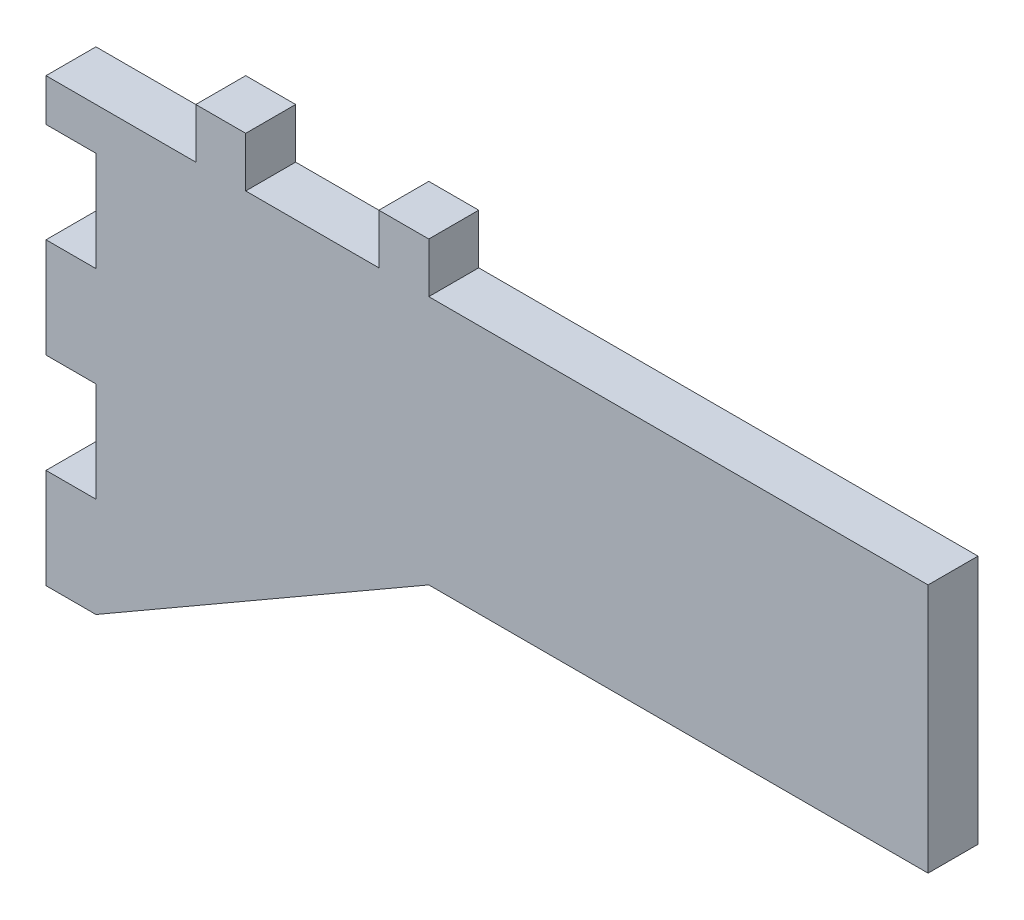
SolidWorks part; units mm, degrees
ref_plane "Front Plane" through (0, 0, 0) normal (0, 0, 1) x (1, 0, 0)
ref_plane "Top Plane" through (0, 0, 0) normal (0, 1, 0) x (1, 0, 0)
ref_plane "Right Plane" through (0, 0, 0) normal (1, 0, 0) x (0, 0, -1)
sketch "Sketch1" plane through (0, 0, 0) normal (0, 0, 1) x (1, 0, 0)
  line L0 (-49.8398, 0) -> (53.8215, 0) construction
  line L1 (0, 44.3135) -> (0, -40.4691) construction
  line L2 (-3, 0) -> (-11, 0)
  line L3 (0, 0) -> (30, 0)
  line L5 (0, -15) -> (30, -15)
  line L6 (30, 0) -> (30, -15)
  line L7 (-20, 0) -> (-20, -26.54)
  line L8 (-20, -26.54) -> (0, -15)
  line L9 (-14, 0) -> (-20, 0)
  line L11 (0, 0) -> (0, 3)
  line L12 (0, 3) -> (-3, 3)
  line L13 (-3, 0) -> (-3, 3)
  line L15 (-11, 0) -> (-11, 3)
  line L16 (-11, 3) -> (-14, 3)
  line L17 (-14, 0) -> (-14, 3)
  point P18 (0, 1.5)
  dimension "D1" = 30
  dimension "D2" = 15
  dimension "D3" = 150.015
  dimension "D4" = 20
  dimension "D5" = 3
  dimension "D6" = 3
  dimension "D7" = 8
  dimension "D8" = 3
  dimension "D9" = 3
extrude "Boss-Extrude1" add sketch "Sketch1" along normal blind 3
sketch "Sketch2" plane through (0, 0, 3) normal (0, 0, 1) x (1, 0, 0)
  line L0 (-20, 0) -> (-20, -26.54) construction
  line L1 (-20, 0) -> (-23, 0)
  line L2 (-20, 0) -> (-20, -2.54)
  line L3 (-20, -2.54) -> (-23, -2.54)
  line L4 (-23, 0) -> (-23, -2.54)
  line L5 (-20, -8.54) -> (-23, -8.54)
  line L6 (-20, -8.54) -> (-20, -14.54)
  line L7 (-20, -14.54) -> (-23, -14.54)
  line L8 (-23, -8.54) -> (-23, -14.54)
  line L10 (-20, -20.54) -> (-23, -20.54)
  line L11 (-20, -20.54) -> (-20, -26.54)
  line L12 (-20, -26.54) -> (-23, -26.54)
  line L13 (-23, -20.54) -> (-23, -26.54)
  point P15 (-21.5, -20.54)
  dimension "D1" = 2.54
  dimension "D2" = 3
  dimension "D3" = 3
  dimension "D4" = 3
  dimension "D5" = 6
  dimension "D6" = 6
  dimension "D7" = 6
  dimension "D8" = 6
extrude "Boss-Extrude2" add sketch "Sketch2" against normal blind 3
sketch "Sketch3" plane through (0, 0, 3) normal (0, 0, 1) x (1, 0, 0)
  line L0 (0, 0) -> (0, -15)
  line L22 (0, 0) -> (0, 3)
  line L23 (0, 3) -> (-3, 3)
  line L24 (-3, 3) -> (-3, 0)
  line L25 (-3, 0) -> (-11, 0)
  line L26 (-11, 0) -> (-11, 3)
  line L27 (-11, 3) -> (-14, 3)
  line L28 (-14, 3) -> (-14, 0)
  line L29 (-14, 0) -> (-23, 0)
  line L30 (-23, 0) -> (-23, -2.54)
  line L31 (-23, -2.54) -> (-20, -2.54)
  line L32 (-20, -2.54) -> (-20, -8.54)
  line L33 (-20, -8.54) -> (-23, -8.54)
  line L34 (-23, -8.54) -> (-23, -14.54)
  line L35 (-23, -14.54) -> (-20, -14.54)
  line L36 (-20, -14.54) -> (-20, -20.54)
  line L37 (-20, -20.54) -> (-23, -20.54)
  line L38 (-23, -20.54) -> (-23, -26.54)
  line L39 (-23, -26.54) -> (-20, -26.54)
  line L40 (-20, -26.54) -> (0, -15)
  line L41 (0, -15) -> (30, -15)
  line L42 (30, -15) -> (30, 0)
  line L43 (30, 0) -> (0, 0)
  line L44 (0, 0) -> (0, 3)
  line L45 (0, 3) -> (-3, 3)
  line L46 (-3, 3) -> (-3, 0)
  line L47 (-3, 0) -> (-11, 0)
  line L48 (-11, 0) -> (-11, 3)
  line L49 (-11, 3) -> (-14, 3)
  line L50 (-14, 3) -> (-14, 0)
  line L51 (-14, 0) -> (-23, 0)
  line L52 (-23, 0) -> (-23, -2.54)
  line L53 (-23, -2.54) -> (-20, -2.54)
  line L54 (-20, -2.54) -> (-20, -8.54)
  line L55 (-20, -8.54) -> (-23, -8.54)
  line L56 (-23, -8.54) -> (-23, -14.54)
  line L57 (-23, -14.54) -> (-20, -14.54)
  line L58 (-20, -14.54) -> (-20, -20.54)
  line L59 (-20, -20.54) -> (-23, -20.54)
  line L60 (-23, -20.54) -> (-23, -26.54)
  line L61 (-23, -26.54) -> (-20, -26.54)
  line L62 (-20, -26.54) -> (0, -15)
  dimension "D1" = 0
